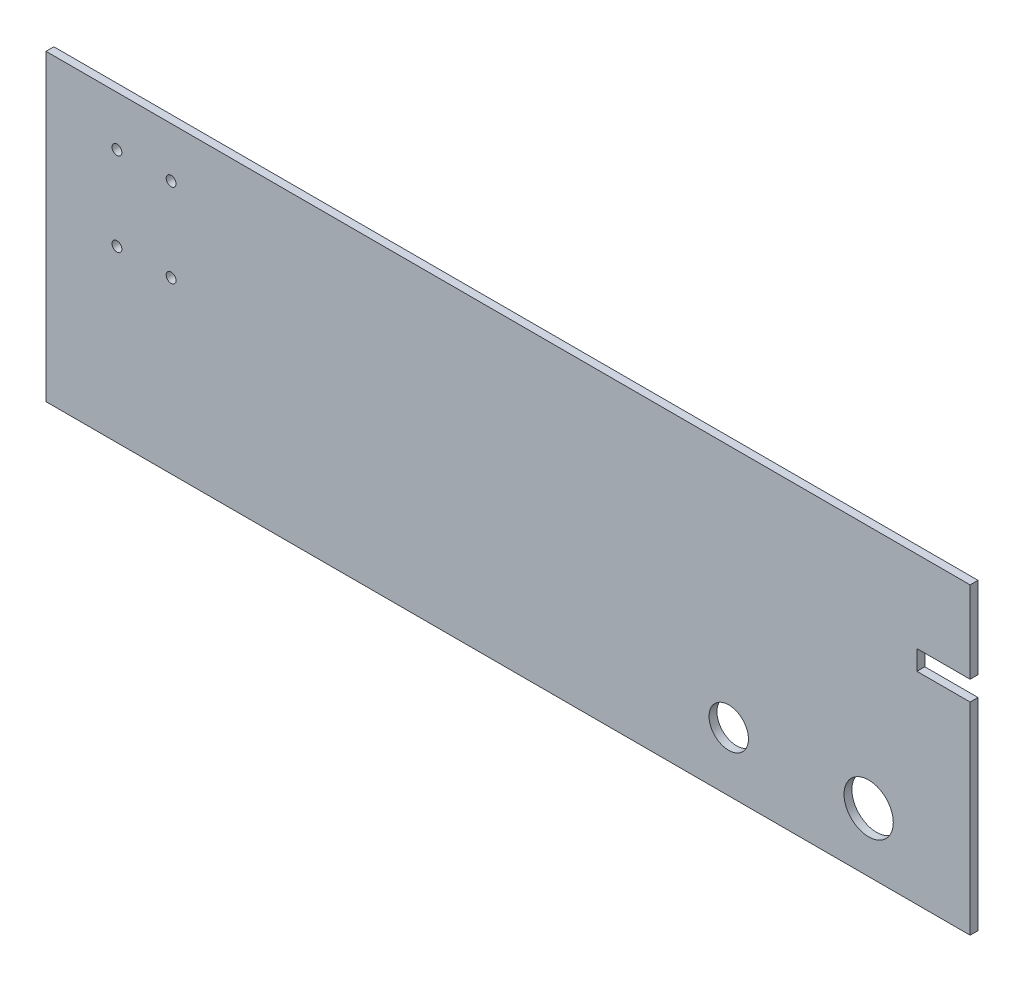
SolidWorks part; units mm, degrees
ref_plane "Plan de face" through (0, 0, 0) normal (0, 0, 1) x (1, 0, 0)
ref_plane "Plan de dessus" through (0, 0, 0) normal (0, 1, 0) x (1, 0, 0)
ref_plane "Plan de droite" through (0, 0, 0) normal (1, 0, 0) x (0, 0, -1)
sketch "EsquisseRef" plane through (0, 0, 0) normal (0, 0, 1) x (1, 0, 0)
  line L0 (-189.5697, 0) -> (273.0097, 0) construction
  line L1 (-693, 248) -> (245, 248)
  line L2 (-693, 248) -> (-693, -60)
  line L3 (-693, -60) -> (245, -60)
  line L4 (245, 248) -> (245, 165)
  line L5 (-660.9323, 155) -> (-26.5265, 155) construction
  line L6 (154.4371, 155) -> (322.7809, 155) construction
  line L7 (-593.5, 205.6722) -> (-593.5, -13.7597) construction
  line L8 (142, 91.4912) -> (142, -41.72) construction
  line L9 (0, 91.4912) -> (0, -41.72) construction
  line L10 (226, 191.0336) -> (226, 50.5031) construction
  line L11 (245, 165) -> (191, 165)
  line L12 (191, 165) -> (191, 145)
  line L13 (245, 145) -> (191, 145)
  line L14 (245, 145) -> (245, -60)
  line L15 (-566, 62.2835) -> (-566, 223.4472) construction
  line L16 (-621, 62.2835) -> (-621, 223.4472) construction
  circle A0 centre (0, 0) radius 20
  circle A1 centre (-621, 197.5) radius 5
  circle A2 centre (-566, 197.5) radius 5
  circle A3 centre (-566, 112.5) radius 5
  circle A4 centre (-621, 112.5) radius 5
  circle A5 centre (142, 0) radius 25
  point P25 (191, 155)
  dimension "D12" = 40
  dimension "D13" = 10
  dimension "D16" = 50
  dimension "D3" = 593.5
  dimension "D2" = 155
  dimension "D4" = 142
  dimension "D17" = 226
  dimension "D5" = 155
  dimension "D6" = 938
  dimension "D7" = 308
  dimension "D8" = 60
  dimension "D9" = 19
  dimension "D10" = 20
  dimension "D11" = 35
  dimension "D14" = 55
  dimension "D15" = 85
extrude "Extrusion1" add sketch "EsquisseRef" against normal blind 8
